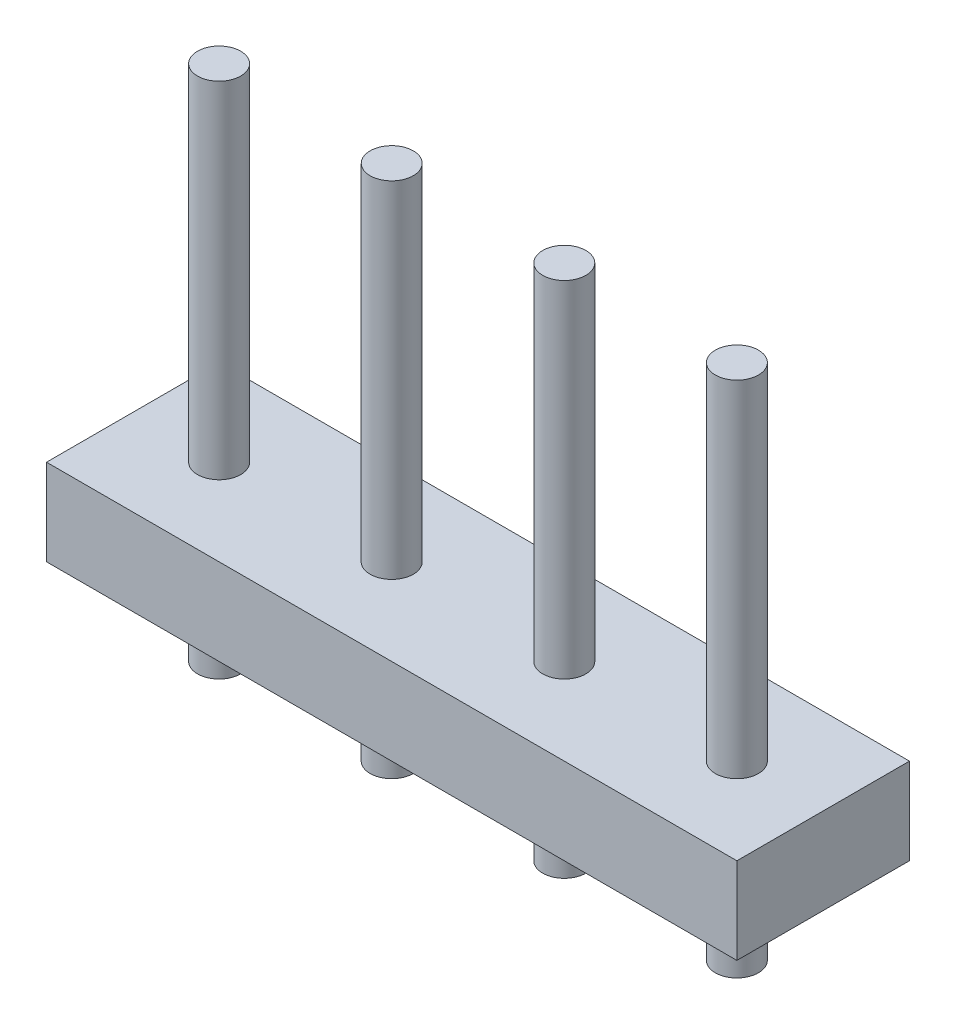
SolidWorks part; units mm, degrees
ref_plane "Front Plane" through (0, 0, 0) normal (0, 0, 1) x (1, 0, 0)
ref_plane "Top Plane" through (0, 0, 0) normal (0, 1, 0) x (1, 0, 0)
ref_plane "Right Plane" through (0, 0, 0) normal (1, 0, 0) x (0, 0, -1)
sketch "Sketch1" plane through (0, 0, 0) normal (0, 1, 0) x (1, 0, 0)
  line L0 (-5.08, -1.27) -> (5.08, 1.27) construction
  line L1 (-5.08, 1.27) -> (5.08, 1.27)
  line L2 (-5.08, 1.27) -> (-5.08, -1.27)
  line L3 (-5.08, -1.27) -> (5.08, -1.27)
  line L4 (5.08, 1.27) -> (5.08, -1.27)
  point P4 (0, 0)
  dimension "D1" = 2.54
  dimension "D2" = 10.16
extrude "Extrude1" add sketch "Sketch1" along normal blind 1.27
sketch "Sketch2" plane through (0, 1.27, 0) normal (0, 1, 0) x (1, 0, 0)
  circle A0 centre (-1.27, 0) radius 0.3175
  circle A1 centre (-3.81, 0) radius 0.3175
  circle A2 centre (1.27, 0) radius 0.3175
  circle A3 centre (3.81, 0) radius 0.3175
  dimension "D1" = 0.635
  dimension "D2" = 0.635
  dimension "D3" = 0.635
  dimension "D4" = 0.635
  dimension "D5" = 1.27
  dimension "D6" = 2.54
  dimension "D7" = 2.54
  dimension "D8" = 2.54
extrude "Extrude2" add sketch "Sketch2" along normal blind 5.08 and the other way blind 2.54
